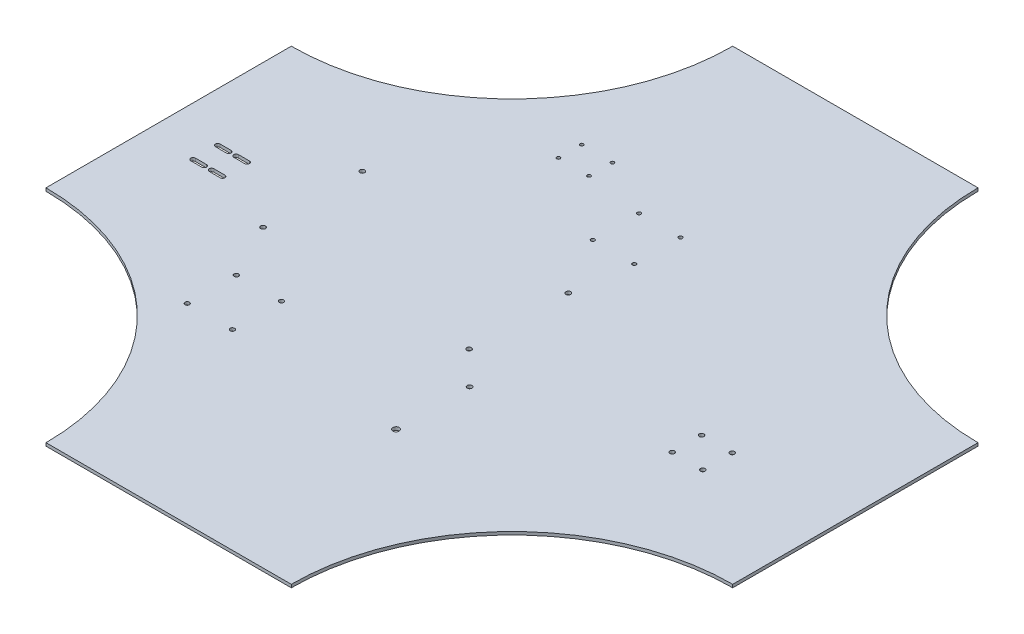
SolidWorks part; units mm, degrees
material "6061 Alloy"
ref_plane "Front Plane" through (0, 0, 0) normal (0, 0, 1) x (1, 0, 0)
ref_plane "Top Plane" through (0, 0, 0) normal (0, 1, 0) x (1, 0, 0)
ref_plane "Right Plane" through (0, 0, 0) normal (1, 0, 0) x (0, 0, -1)
sketch "Sketch1" plane through (0, 0, 0) normal (0, 1, 0) x (1, 0, 0)
  line L9 (-127, -355.6) -> (127, -355.6)
  line L10 (-355.6, -127) -> (-355.6, 127)
  line L11 (-127, 355.6) -> (127, 355.6)
  line L12 (355.6, -127) -> (355.6, 127)
  line L13 (-193.9554, -193.9554) -> (193.9554, 193.9554) construction
  line L14 (-193.9554, 193.9554) -> (193.9554, -193.9554) construction
  arc A8 (-355.6, 127) -> (-127, 355.6) centre (-355.6, 355.6) ccw
  arc A9 (127, 355.6) -> (355.6, 127) centre (355.6, 355.6) ccw
  arc A10 (355.6, -127) -> (127, -355.6) centre (355.6, -355.6) ccw
  arc A11 (-127, -355.6) -> (-355.6, -127) centre (-355.6, -355.6) ccw
  point P0 (0, 0)
  point P1 (0, 0)
  point P2 (0, 0)
  dimension "D3" = 457.2
  dimension "D4" = 457.2
  dimension "D5" = 457.2
  dimension "D6" = 457.2
  dimension "D1" = 711.2
  dimension "D2" = 711.2
extrude "Boss-Extrude1" add sketch "Sketch1" along normal blind 3.175
sketch "Sketch2" plane through (0, 3.175, 0) normal (0, 1, 0) x (1, 0, 0)
  line L0 (-304.8, 2.413) -> (-293.37, 2.413)
  line L1 (-304.8, -22.987) -> (-293.37, -22.987)
  line L2 (-293.37, -2.413) -> (-304.8, -2.413)
  line L3 (-285.75, -2.413) -> (-274.32, -2.413)
  line L4 (-285.75, -22.987) -> (-274.32, -22.987)
  line L5 (-274.32, 2.413) -> (-285.75, 2.413)
  line L6 (-293.37, -27.813) -> (-304.8, -27.813)
  line L7 (-355.6, 127) -> (-355.6, -127) construction
  line L8 (-274.32, -27.813) -> (-285.75, -27.813)
  arc A0 (-293.37, -2.413) -> (-293.37, 2.413) centre (-293.37, 0) ccw
  arc A1 (-274.32, -2.413) -> (-274.32, 2.413) centre (-274.32, 0) ccw
  arc A2 (-274.32, -27.813) -> (-274.32, -22.987) centre (-274.32, -25.4) ccw
  arc A3 (-293.37, -27.813) -> (-293.37, -22.987) centre (-293.37, -25.4) ccw
  arc A4 (-285.75, 2.413) -> (-285.75, -2.413) centre (-285.75, 0) ccw
  arc A5 (-304.8, 2.413) -> (-304.8, -2.413) centre (-304.8, 0) ccw
  arc A6 (-304.8, -22.987) -> (-304.8, -27.813) centre (-304.8, -25.4) ccw
  arc A7 (-285.75, -22.987) -> (-285.75, -27.813) centre (-285.75, -25.4) ccw
  dimension "D1" = 4.826
  dimension "D2" = 4.826
  dimension "D3" = 4.826
  dimension "D4" = 4.826
  dimension "D5" = 4.826
  dimension "D6" = 4.826
  dimension "D7" = 4.826
  dimension "D8" = 4.826
  dimension "D9" = 11.43
  dimension "D10" = 11.43
  dimension "D11" = 11.43
  dimension "D12" = 11.43
  dimension "D13" = 19.05
  dimension "D14" = 19.05
  dimension "D15" = 25.4
  dimension "D16" = 25.4
  dimension "D17" = 0
  dimension "D18" = 50.8
extrude "Cut-Extrude1" cut sketch "Sketch2" against normal through all both and the other way through all
sketch "Sketch4" plane through (0, 3.175, 0) normal (0, 1, 0) x (1, 0, 0)
  circle A0 centre (237.49, -9.4302) radius 2.413
  circle A1 centre (205.74, -9.4302) radius 2.413
  circle A2 centre (237.49, -39.9102) radius 2.413
  circle A3 centre (205.74, -39.9102) radius 2.413
extrude "Cut-Extrude2" cut sketch "Sketch4" against normal through all
sketch "Sketch5" plane through (0, 0, 0) normal (0, -1, 0) x (1, 0, 0)
  circle A0 centre (-207.7901, 50.0166) radius 2.5
  circle A1 centre (-206.624, -51.5767) radius 2.5
  circle A2 centre (8.0956, 52.4945) radius 2.478
  circle A3 centre (9.2617, -49.0988) radius 2.5
extrude "Cut-Extrude3" cut sketch "Sketch5" against normal through all
sketch "Sketch6" plane through (0, 0, 0) normal (0, -1, 0) x (1, 0, 0)
  circle A0 centre (-131.9657, 157.5947) radius 2.3218
  circle A1 centre (-131.9657, 106.7947) radius 2.3218
  circle A2 centre (-178.7006, 106.7947) radius 2.3218
  circle A3 centre (-178.7006, 157.5947) radius 2.3218
  circle A4 centre (42.2659, 162.3375) radius 3.2723
  circle A5 centre (42.2659, 86.1375) radius 2.5
  circle A6 centre (17.3717, -109.2657) radius 1.905
  circle A7 centre (-25.6811, -109.3842) radius 1.905
  circle A8 centre (-25.5498, -157.136) radius 1.905
  circle A9 centre (17.503, -157.0152) radius 1.905
  circle A10 centre (-84.8824, -188.8713) radius 1.75
  circle A11 centre (-85.0918, -164.8722) radius 1.75
  circle A12 centre (-116.8812, -189.1505) radius 1.75
  circle A13 centre (-117.0906, -165.1514) radius 1.75
extrude "Cut-Extrude4" cut sketch "Sketch6" against normal through all
